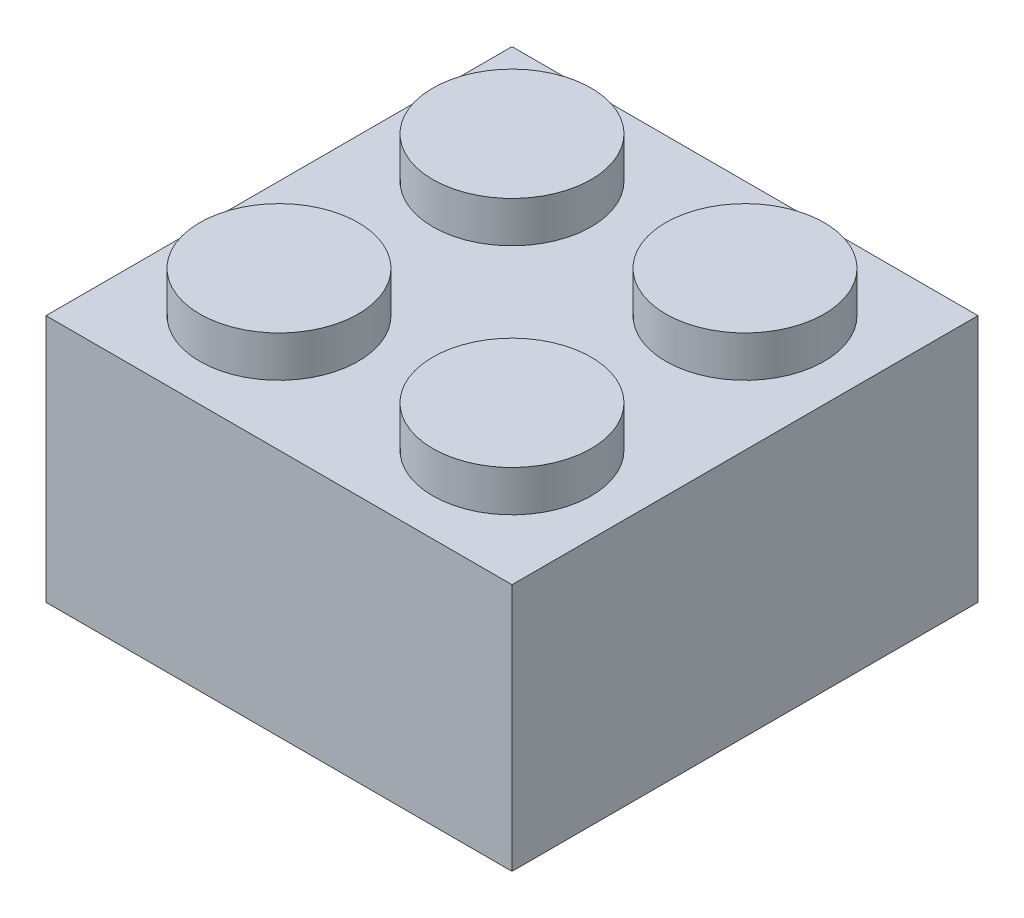
SolidWorks part; units mm, degrees
ref_plane "Front Plane" through (0, 0, 0) normal (0, 0, 1) x (1, 0, 0)
ref_plane "Top Plane" through (0, 0, 0) normal (0, 1, 0) x (1, 0, 0)
ref_plane "Right Plane" through (0, 0, 0) normal (1, 0, 0) x (0, 0, -1)
sketch "Sketch1" plane through (0, 0, 0) normal (0, 1, 0) x (1, 0, 0)
  line L1 (-7.9375, 7.9375) -> (7.9375, 7.9375)
  line L2 (-7.9375, 7.9375) -> (-7.9375, -7.9375)
  line L3 (-7.9375, -7.9375) -> (7.9375, -7.9375)
  line L4 (7.9375, 7.9375) -> (7.9375, -7.9375)
  line L5 (-7.9375, 7.9375) -> (7.9375, -7.9375) construction
  line L6 (-7.9375, -7.9375) -> (7.9375, 7.9375) construction
  point P0 (0, 0)
  dimension "D1" = 15.875
extrude "Boss-Extrude1" add sketch "Sketch1" along normal mid plane 8.4582
sketch "Sketch2" plane through (0, -4.2291, 0) normal (0, -1, 0) x (1, 0, 0)
  line L12 (6.6675, -6.6675) -> (6.6675, 6.6675)
  line L13 (6.6675, 6.6675) -> (-6.6675, 6.6675)
  line L14 (-6.6675, 6.6675) -> (-6.6675, -6.6675)
  line L15 (-6.6675, -6.6675) -> (6.6675, -6.6675)
  line L16 (6.6675, -6.6675) -> (6.6675, 6.6675)
  line L17 (6.6675, 6.6675) -> (-6.6675, 6.6675)
  line L18 (-6.6675, 6.6675) -> (-6.6675, -6.6675)
  line L19 (-6.6675, -6.6675) -> (6.6675, -6.6675)
  circle A0 centre (0, 0) radius 3.175
  circle A1 centre (0, 0) radius 2.413
  dimension "D2" = 6.35
  dimension "D3" = 0.762
  dimension "D1" = 1.27
extrude "Cut-Extrude1" cut sketch "Sketch2" against normal offset from surface (7.1882 mm away) 1.27 contours L18 L19 L16 L17 A0 | A1 up to face at (0, 4.2291, 0)
sketch "Sketch3" plane through (0, 4.2291, 0) normal (0, 1, 0) x (1, 0, 0)
  line L0 (-6.6675, -6.6675) -> (-6.6675, 6.6675) construction
  line L1 (6.6675, -6.6675) -> (-6.6675, -6.6675) construction
  line L2 (6.6675, 6.6675) -> (6.6675, -6.6675) construction
  line L3 (-6.6675, 6.6675) -> (6.6675, 6.6675) construction
  line L4 (-6.6675, -6.6675) -> (-6.6675, 6.6675) construction
  line L5 (6.6675, -6.6675) -> (-6.6675, -6.6675) construction
  line L6 (6.6675, 6.6675) -> (6.6675, -6.6675) construction
  line L7 (-6.6675, 6.6675) -> (6.6675, 6.6675) construction
  line L8 (1.27, -6.6675) -> (1.27, -1.27) construction
  line L9 (3.9687, 3.9688) -> (-3.9687, 3.9688) construction
  line L10 (3.9687, 3.9688) -> (3.9687, -3.9688) construction
  line L11 (3.9687, -3.9688) -> (-3.9687, -3.9688) construction
  line L12 (-3.9687, 3.9688) -> (-3.9687, -3.9688) construction
  line L13 (3.9687, 3.9688) -> (-3.9687, -3.9688) construction
  line L14 (3.9687, -3.9688) -> (-3.9687, 3.9688) construction
  line L15 (1.27, -1.27) -> (6.6675, -1.27) construction
  line L16 (0, -4.652) -> (0, 4.652) construction
  circle A0 centre (3.9687, -3.9688) radius 2.6987
  circle A1 centre (3.9687, 3.9688) radius 2.6987
  circle A2 centre (-3.9687, -3.9688) radius 2.6987
  circle A3 centre (-3.9687, 3.9688) radius 2.6987
  point P4 (0, 0)
  point P16 (-6.6675, 3.9688)
  point P17 (-3.9687, 6.6675)
  point P19 (1.27, -3.9688)
  point P20 (3.9687, -1.27)
  dimension "D1" = 1.27
extrude "Boss-Extrude2" add sketch "Sketch3" along normal blind 1.397
